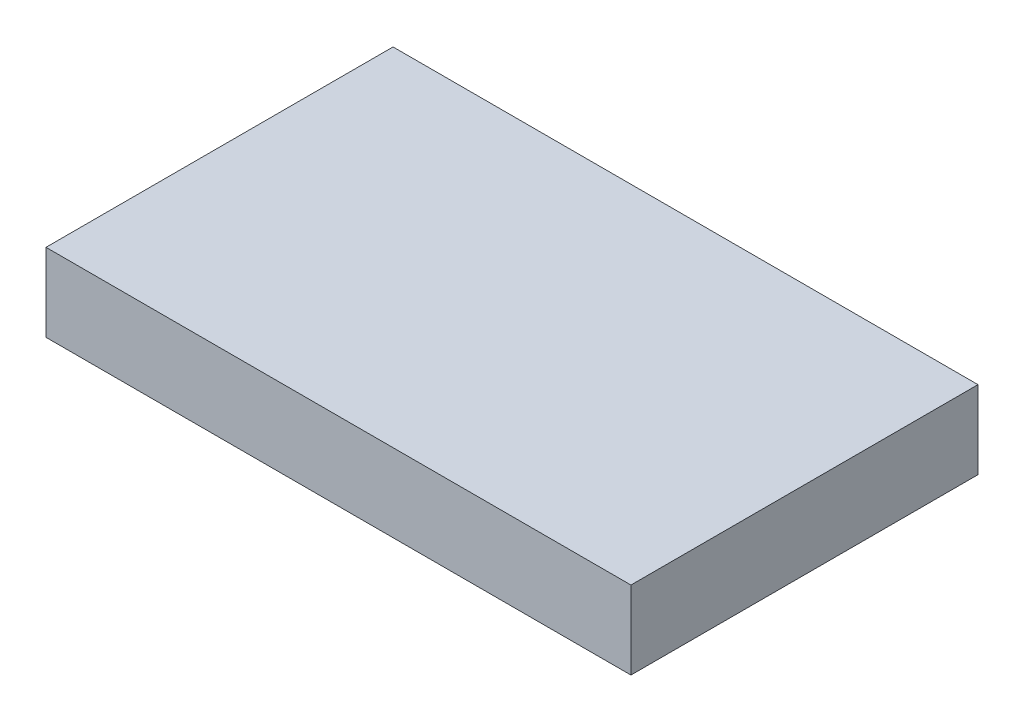
SolidWorks part; units mm, degrees
ref_plane "Front Plane" through (0, 0, 0) normal (0, 0, 1) x (1, 0, 0)
ref_plane "Top Plane" through (0, 0, 0) normal (0, 1, 0) x (1, 0, 0)
ref_plane "Right Plane" through (0, 0, 0) normal (1, 0, 0) x (0, 0, -1)
sketch "Sketch1" plane through (0, 0, 0) normal (0, 1, 0) x (1, 0, 0)
  line L1 (0, 0) -> (150, 0)
  line L2 (0, 0) -> (0, 89)
  line L3 (0, 89) -> (150, 89)
  line L4 (150, 0) -> (150, 89)
  dimension "D1" = 150
  dimension "D2" = 89
extrude "Boss-Extrude1" add sketch "Sketch1" along normal blind 20
